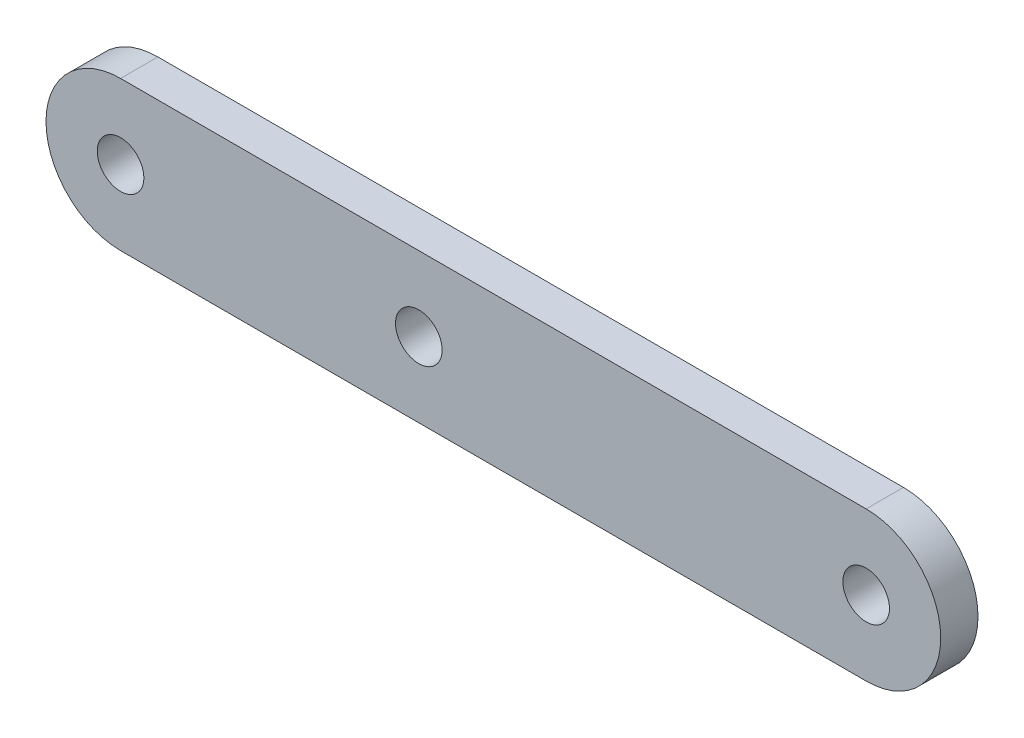
SolidWorks part; units mm, degrees
ref_plane "Front Plane" through (0, 0, 0) normal (0, 0, 1) x (1, 0, 0)
ref_plane "Top Plane" through (0, 0, 0) normal (0, 1, 0) x (1, 0, 0)
ref_plane "Right Plane" through (0, 0, 0) normal (1, 0, 0) x (0, 0, -1)
sketch "Sketch1" plane through (0, 0, 0) normal (0, 0, 1) x (1, 0, 0)
  line L1 (20, -4) -> (-20, -4)
  line L3 (20, 4) -> (-20, 4)
  line L5 (20, -4) -> (-20, 4) construction
  line L6 (20, 4) -> (-20, -4) construction
  arc A0 (20, 4) -> (20, -4) centre (20, 0) cw
  arc A1 (-20, 4) -> (-20, -4) centre (-20, 0) ccw
  circle A2 centre (-20, 0) radius 1.25
  circle A3 centre (20, 0) radius 1.25
  circle A4 centre (-4, 0) radius 1.25
  point P0 (0, 0)
  dimension "D3" = 2.5
  dimension "D1" = 40
  dimension "D2" = 8
  dimension "D4" = 16
extrude "Extrude1" add sketch "Sketch1" along normal blind 2
